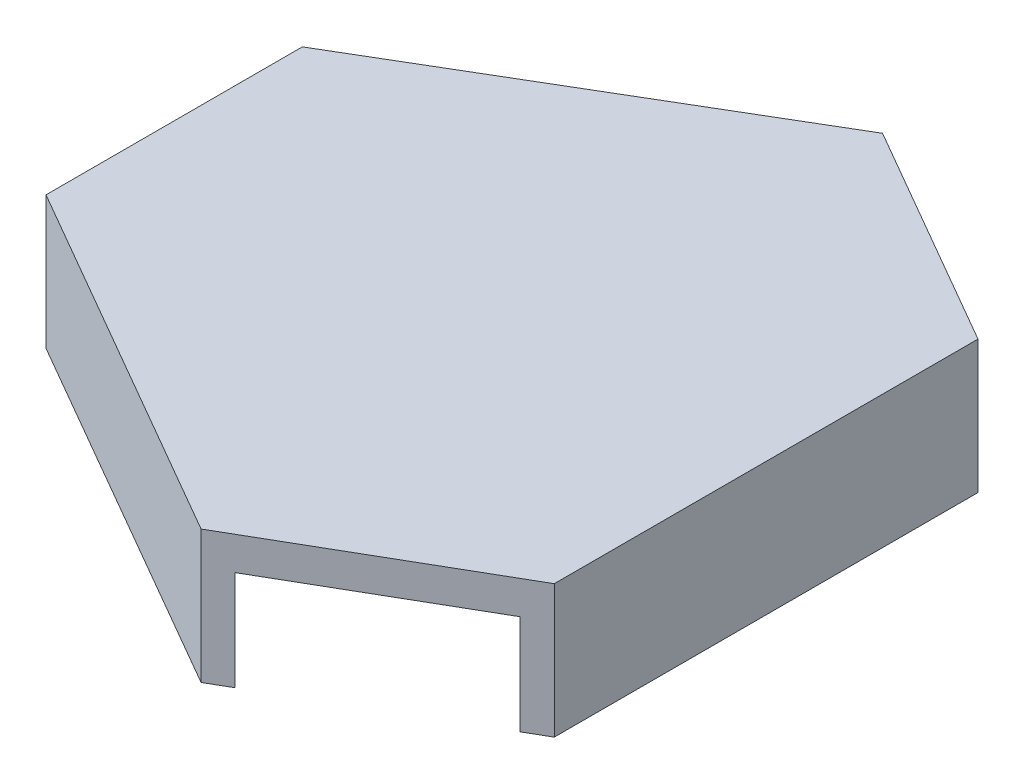
SolidWorks part; units mm, degrees
material "Polyester Resin"
ref_plane "Front Plane" through (0, 0, 0) normal (0, 0, 1) x (1, 0, 0)
ref_plane "Top Plane" through (0, 0, 0) normal (0, 1, 0) x (1, 0, 0)
ref_plane "Right Plane" through (0, 0, 0) normal (1, 0, 0) x (0, 0, -1)
sketch "Sketch3" plane through (0, 0, 0) normal (0, 1, 0) x (1, 0, 0)
  line L7 (-9.1401, 3.8223) -> (1.8418, 10.3)
  line L12 (-9.1401, -3.8912) -> (1.9017, -10.2662)
  line L16 (8.6405, -6.3766) -> (8.6416, 6.3734)
  line L21 (-9.1401, 3.8223) -> (-9.1401, -3.8912)
  line L22 (1.8418, 10.3) -> (8.6416, 6.3734)
  line L23 (8.6405, -6.3766) -> (1.9017, -10.2662)
  dimension "D2" = 12.75
extrude "Boss-Extrude2" add sketch "Sketch3" along normal blind 1
sketch "Sketch5" plane through (0, 0, 0) normal (0, -1, 0) x (1, 0, 0)
  line L0 (-9.1401, 3.8912) -> (1.9017, 10.2662)
  line L1 (1.9017, 10.2662) -> (2.5512, 9.8913)
  line L2 (1.9017, 10.2662) -> (8.6405, 6.3766) construction
  line L3 (2.5512, 9.8913) -> (-9.1401, 3.1413)
  line L4 (-9.1401, -3.8223) -> (-9.1401, 3.8912) construction
  line L5 (-9.1401, 3.1413) -> (-9.1401, 3.8912)
  line L6 (-9.1401, -3.8223) -> (-9.1401, -3.0683)
  line L7 (-9.1401, -3.0683) -> (2.4878, -9.927)
  line L8 (8.6416, -6.3734) -> (1.8418, -10.3) construction
  line L9 (2.4878, -9.927) -> (1.8418, -10.3)
  line L10 (1.8418, -10.3) -> (-9.1401, -3.8223)
  line L11 (8.6405, 6.3766) -> (8.6416, -6.3734)
  line L12 (8.6416, -6.3734) -> (7.9921, -6.7484)
  line L13 (7.9921, -6.7484) -> (7.9909, 6.7516)
  line L14 (7.9909, 6.7516) -> (8.6405, 6.3766)
  dimension "D1" = 13.5
  dimension "D2" = 13.5
  dimension "D3" = 13.5
extrude "Boss-Extrude3" add sketch "Sketch5" along normal blind 3
